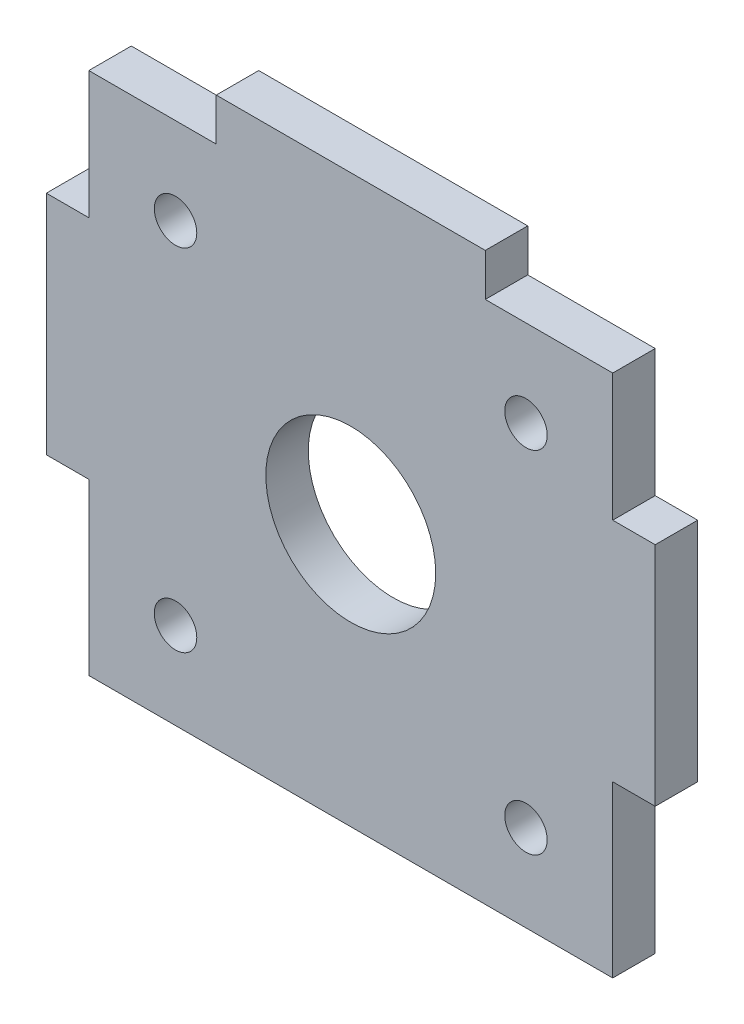
SolidWorks part; units mm, degrees
ref_plane "Front Plane" through (0, 0, 0) normal (0, 0, 1) x (1, 0, 0)
ref_plane "Top Plane" through (0, 0, 0) normal (0, 1, 0) x (1, 0, 0)
ref_plane "Right Plane" through (0, 0, 0) normal (1, 0, 0) x (0, 0, -1)
sketch "Sketch1" plane through (0, 0, 0) normal (0, 0, 1) x (1, 0, 0)
  line L0 (-12.3744, 12.3744) -> (12.3744, -12.3744) construction
  line L1 (-21.5, 21.5) -> (21.5, 21.5)
  line L2 (-21.5, 21.5) -> (-21.5, -21.5)
  line L3 (-21.5, -21.5) -> (21.5, -21.5)
  line L4 (21.5, 21.5) -> (21.5, -21.5)
  line L5 (-21.5, 21.5) -> (21.5, -21.5) construction
  line L6 (-21.5, -21.5) -> (21.5, 21.5) construction
  line L7 (12.3744, 12.3744) -> (-12.3744, -12.3744) construction
  circle A0 centre (-12.3744, 12.3744) radius 1.5
  circle A1 centre (12.3744, -12.3744) radius 1.5
  circle A2 centre (12.3744, 12.3744) radius 1.5
  circle A3 centre (-12.3744, -12.3744) radius 1.5
  circle A4 centre (0, 0) radius 6
  point P0 (0, 0)
  point P9 (0, 0)
  point P12 (0, 0)
  dimension "D1" = 3
  dimension "D6" = 12
  dimension "D2" = 17.5
  dimension "D3" = 45
  dimension "D4" = 43
  dimension "D5" = 43
extrude "Boss-Extrude1" add sketch "Sketch1" along normal blind 3
sketch "Sketch2" plane through (0, 0, 3) normal (0, 0, 1) x (1, 0, 0)
  line L0 (21.5, -21.5) -> (21.5, 21.5) construction
  line L1 (-21.5, -21.5) -> (21.5, -21.5)
  line L2 (-21.5, -21.5) -> (-21.5, -18.5)
  line L3 (-18.5, -18.5) -> (18.5, -18.5)
  line L4 (21.5, -21.5) -> (21.5, -18.5)
  line L5 (-21.5, 9.5) -> (-18.5, 9.5)
  line L6 (-21.5, 21.5) -> (-21.5, -21.5) construction
  line L7 (-18.5, 9.5) -> (-18.5, 18.5)
  line L8 (-18.5, 18.5) -> (-9.5, 18.5)
  line L9 (-9.5, 18.5) -> (-9.5, 21.5)
  line L10 (21.5, 21.5) -> (-21.5, 21.5) construction
  line L11 (-21.5, 9.5) -> (-21.5, 21.5)
  line L12 (-21.5, 21.5) -> (-9.5, 21.5)
  line L13 (0, 0) -> (0, -3.5321) construction
  line L14 (21.5, 9.5) -> (21.5, 21.5)
  line L15 (21.5, 9.5) -> (18.5, 9.5)
  line L16 (18.5, 9.5) -> (18.5, 18.5)
  line L17 (18.5, 18.5) -> (9.5, 18.5)
  line L18 (9.5, 18.5) -> (9.5, 21.5)
  line L19 (21.5, 21.5) -> (9.5, 21.5)
  line L20 (-21.5, -18.5) -> (-18.5, -18.5) construction
  line L21 (-21.5, -18.5) -> (-18.5, -18.5) construction
  line L22 (-21.5, -18.5) -> (-21.5, -6.5)
  line L23 (-21.5, -6.5) -> (-18.5, -6.5)
  line L24 (-18.5, -18.5) -> (-18.5, -6.5)
  line L25 (21.5, -18.5) -> (18.5, -18.5) construction
  line L26 (21.5, -18.5) -> (21.5, -6.5)
  line L27 (21.5, -6.5) -> (18.5, -6.5)
  line L28 (18.5, -18.5) -> (18.5, -6.5)
  line L29 (18.5, -18.5) -> (21.5, -18.5) construction
  dimension "D1" = 3
  dimension "D2" = 3
  dimension "D3" = 3
  dimension "D4" = 12
  dimension "D5" = 12
  dimension "D6" = 3
  dimension "D7" = 12
extrude "Cut-Extrude1" cut sketch "Sketch2" against normal blind 3
